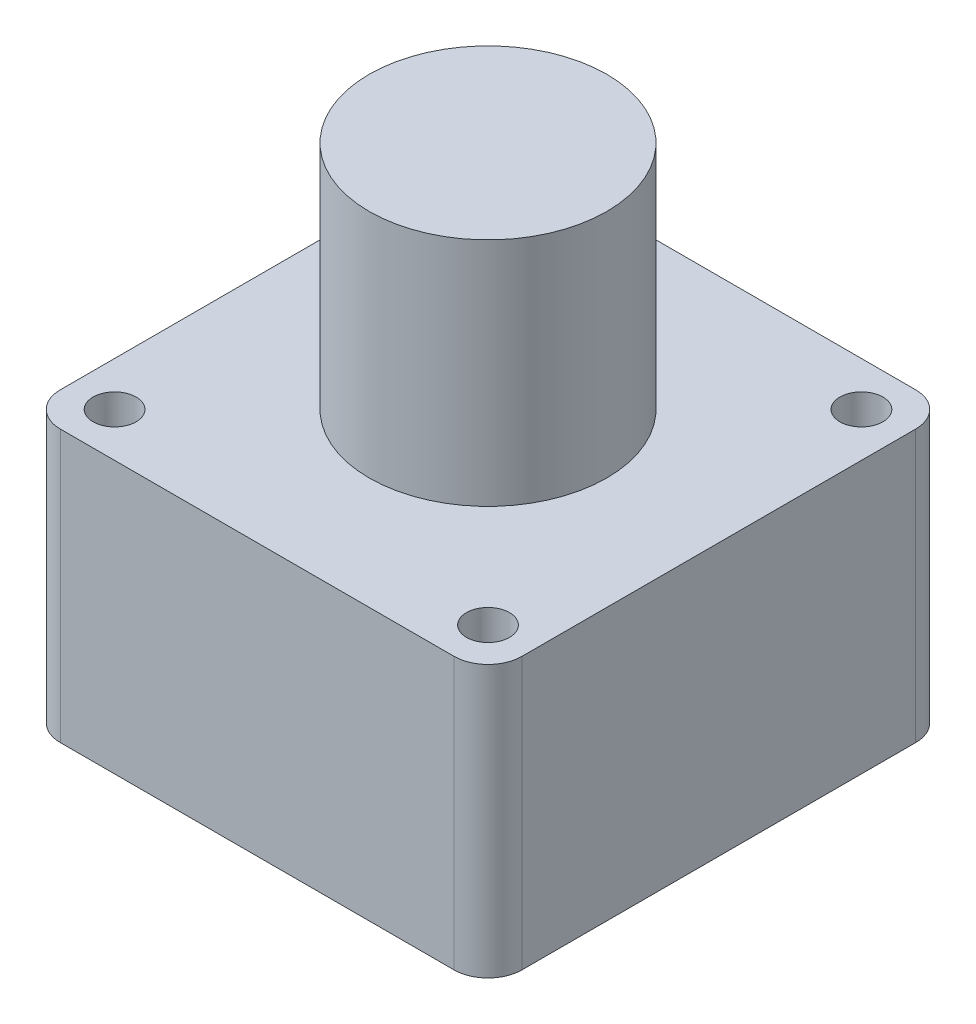
SolidWorks part; units mm, degrees
ref_plane "Front Plane" through (0, 0, 0) normal (0, 0, 1) x (1, 0, 0)
ref_plane "Top Plane" through (0, 0, 0) normal (0, 1, 0) x (1, 0, 0)
ref_plane "Right Plane" through (0, 0, 0) normal (1, 0, 0) x (0, 0, -1)
sketch "Sketch1" plane through (0, 0, 0) normal (0, 1, 0) x (1, 0, 0)
  line L1 (-29, 34) -> (29, 34)
  line L2 (-34, 29) -> (-34, -29)
  line L3 (-29, -34) -> (29, -34)
  line L4 (34, 29) -> (34, -29)
  arc A0 (29, -34) -> (34, -29) centre (29, -29) ccw
  arc A1 (-34, -29) -> (-29, -34) centre (-29, -29) ccw
  arc A2 (29, 34) -> (34, 29) centre (29, 29) cw
  arc A3 (-29, 34) -> (-34, 29) centre (-29, 29) ccw
  point P4 (-34, 0)
  point P5 (0, 34)
  point P11 (-34, -34)
  point P16 (-34, 34)
  dimension "D2" = 5
  dimension "D1" = 68
extrude "Boss-Extrude1" add sketch "Sketch1" along normal blind 40 contours L2 A1 L3 A0 L4 A2 L1 A3
sketch "Sketch2" plane through (0, 40, 0) normal (0, 1, 0) x (1, 0, 0)
  circle A0 centre (0, 0) radius 17.5
  dimension "D1" = 35
extrude "Boss-Extrude2" add sketch "Sketch2" along normal blind 34
sketch "Sketch3" plane through (0, 40, 0) normal (0, 1, 0) x (1, 0, 0)
  line L0 (-51.7219, 0) -> (58.4879, 0) construction
  line L1 (0, 43.0003) -> (0, -45.4197) construction
  circle A0 centre (-27.5, 27.5) radius 3.1675
  circle A1 centre (-27.5, -27.5) radius 3.1675
  circle A2 centre (27.5, -27.5) radius 3.1675
  circle A3 centre (27.5, 27.5) radius 3.1675
  dimension "D1" = 27.5
  dimension "D3" = 6.335
  dimension "D2" = 27.5
extrude "Cut-Extrude1" cut sketch "Sketch3" against normal up to next
